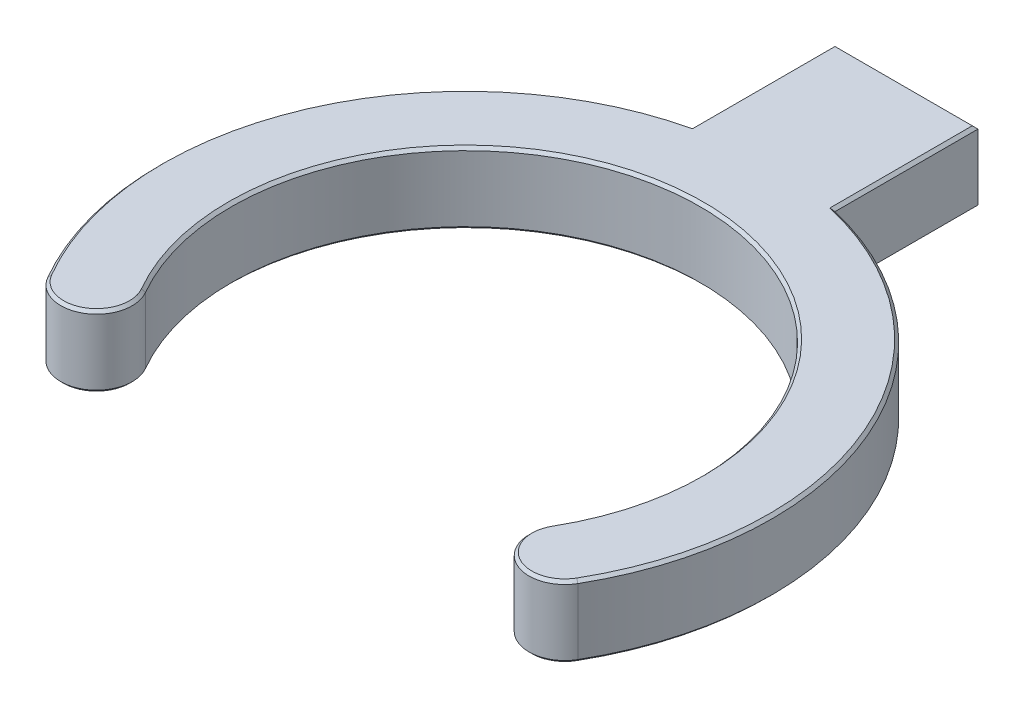
SolidWorks part; units mm, degrees
ref_plane "Front Plane" through (0, 0, 0) normal (0, 0, 1) x (1, 0, 0)
ref_plane "Top Plane" through (0, 0, 0) normal (0, 1, 0) x (1, 0, 0)
ref_plane "Right Plane" through (0, 0, 0) normal (1, 0, 0) x (0, 0, -1)
sketch "Sketch1" plane through (0, 0, 0) normal (0, 1, 0) x (1, 0, 0)
  line L0 (0, 0) -> (-33.2598, -19.2026) construction
  line L1 (0, 41.4651) -> (0, -29.5882) construction
  line L2 (0, 0) -> (35.8524, -20.6994) construction
  line L4 (-5, 30.8077) -> (5, 30.8077)
  line L5 (-5, 30.8077) -> (-5, 20.8077)
  line L7 (5, 30.8077) -> (5, 20.8077)
  arc A0 (14.2028, -8.2) -> (-14.2028, -8.2) centre (0, 0) ccw
  arc A1 (18.5329, -10.7) -> (5, 20.8077) centre (0, 0) ccw
  arc A2 (-18.5329, -10.7) -> (-14.2028, -8.2) centre (-16.3679, -9.45) ccw
  arc A3 (14.2028, -8.2) -> (18.5329, -10.7) centre (16.3679, -9.45) ccw
  arc A4 (-5, 20.8077) -> (-18.5329, -10.7) centre (0, 0) ccw
  point P16 (0, 41.4651)
  point P17 (0, 30.8077)
  dimension "D1" = 32.8
  dimension "D2" = 5
  dimension "D3" = 60
  dimension "D4" = 60
  dimension "D5" = 10
  dimension "D6" = 10
extrude "Boss-Extrude1" add sketch "Sketch1" along normal blind 5
chamfer "Chamfer1" distance 0.2 angle 45 16 edges at (-15.1179, 0, 11.6151) (0, 0, -16.4) (15.1179, 0, 11.6151) (19.663, 0, -8.4455) (5, 0, -25.8077) (0, 0, -30.8077) (-5, 0, -25.8077) (-19.663, 0, -8.4455) (-5, 5, -25.8077) (0, 5, -30.8077) (5, 5, -25.8077) (19.663, 5, -8.4455) (15.1179, 5, 11.6151) (0, 5, -16.4) (-15.1179, 5, 11.6151) (-19.663, 5, -8.4455)
